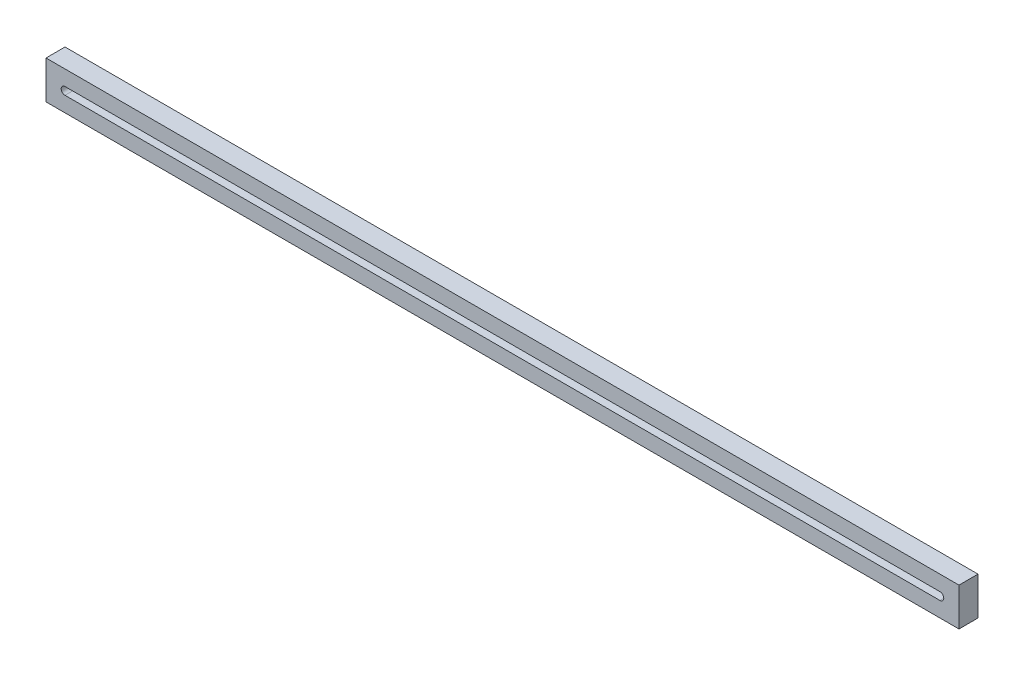
SolidWorks part; units mm, degrees
ref_plane "Front Plane" through (0, 0, 0) normal (0, 0, 1) x (1, 0, 0)
ref_plane "Top Plane" through (0, 0, 0) normal (0, 1, 0) x (1, 0, 0)
ref_plane "Right Plane" through (0, 0, 0) normal (1, 0, 0) x (0, 0, -1)
sketch "Sketch1" plane through (0, 0, 0) normal (0, 0, 1) x (1, 0, 0)
  line L1 (-152.4, 6.35) -> (152.4, 6.35)
  line L2 (-152.4, 6.35) -> (-152.4, -6.35)
  line L3 (-152.4, -6.35) -> (152.4, -6.35)
  line L4 (152.4, 6.35) -> (152.4, -6.35)
  line L5 (-152.4, 6.35) -> (152.4, -6.35) construction
  line L6 (-152.4, -6.35) -> (152.4, 6.35) construction
  line L7 (-146.05, 1.27) -> (146.05, 1.27)
  line L8 (-146.05, 1.27) -> (-146.05, -1.27)
  line L9 (-146.05, -1.27) -> (146.05, -1.27)
  line L10 (146.05, 1.27) -> (146.05, -1.27)
  line L11 (-146.05, 1.27) -> (146.05, -1.27) construction
  line L12 (-146.05, -1.27) -> (146.05, 1.27) construction
  circle A0 centre (-146.05, 0) radius 1.27
  circle A1 centre (146.05, 0) radius 1.27
  point P0 (0, 0)
  point P5 (0, 0)
  point P15 (0, 0)
  point P16 (-146.05, 0)
  point P17 (0, 0)
  point P18 (146.05, 0)
  dimension "D5" = 2.54
  dimension "D6" = 2.54
  dimension "D1" = 12.7
  dimension "D2" = 304.8
  dimension "D3" = 2.54
  dimension "D4" = 292.1
extrude "Boss-Extrude1" add sketch "Sketch1" along normal blind 6.35 contours L4 L1 L2 L3 A1 L9 A0 L7
